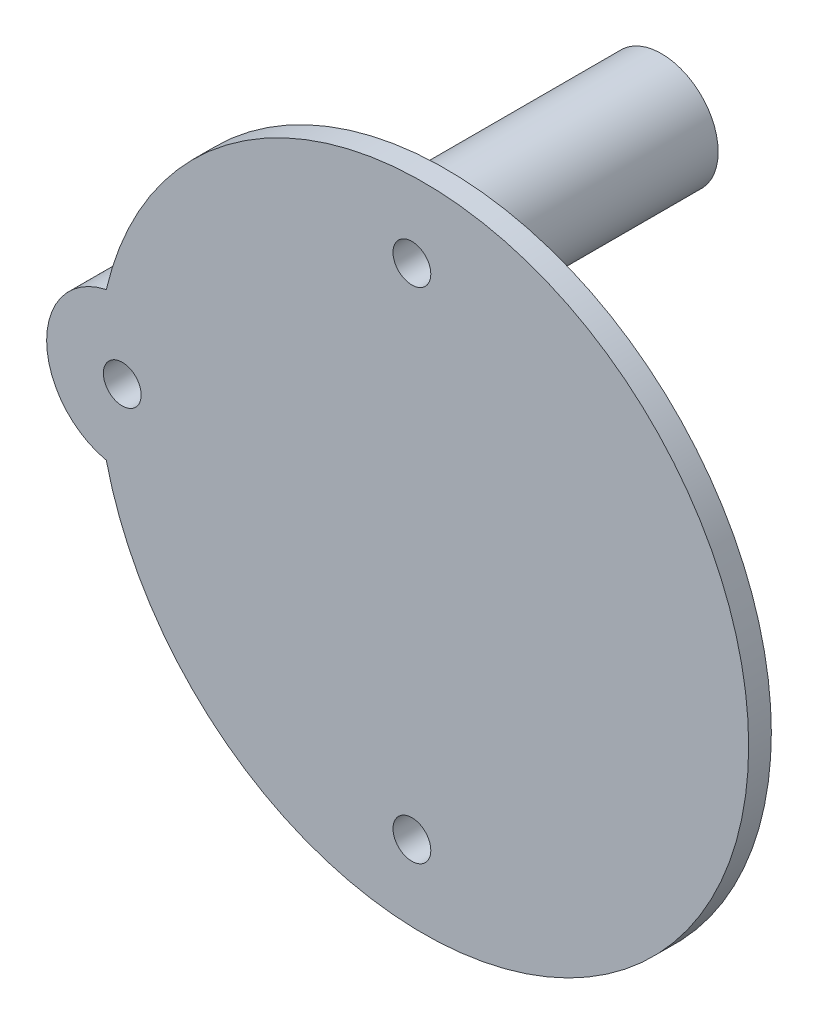
SolidWorks part; units mm, degrees
ref_plane "Front Plane" through (0, 0, 0) normal (0, 0, 1) x (1, 0, 0)
ref_plane "Top Plane" through (0, 0, 0) normal (0, 1, 0) x (1, 0, 0)
ref_plane "Right Plane" through (0, 0, 0) normal (1, 0, 0) x (0, 0, -1)
sketch "Sketch1" plane through (0, 0, 0) normal (0, 0, 1) x (1, 0, 0)
  circle A23 centre (29, 12) radius 5
  circle A24 centre (29, 12) radius 5
  circle A26 centre (-9.3, 45) radius 5
  circle A27 centre (-9.3, 45) radius 5
  circle A28 centre (29, 78) radius 7.5
  circle A29 centre (29, 78) radius 5
  circle A30 centre (29, 78) radius 5
  circle A31 centre (-9.3, 45) radius 10
  circle A34 centre (29, 12) radius 7
  dimension "D6" = 14
  dimension "D1" = 0.5
  dimension "D2" = 0.5
  dimension "D3" = 0.5
  dimension "D4" = 2.5
  dimension "D5" = 5
extrude "Boss-Extrude1" add sketch "Sketch1" along normal blind 3
sketch "Sketch3" plane through (0, 0, 3) normal (0, 0, 1) x (1, 0, 0)
  circle A0 centre (29, 12) radius 7 construction
  circle A1 centre (29, 78) radius 7.5 construction
  circle A2 centre (-9.3, 45) radius 10 construction
  circle A3 centre (29, 12) radius 7
  circle A4 centre (29, 78) radius 7.5
  circle A5 centre (-9.3, 45) radius 10
extrude "Boss-Extrude2" add sketch "Sketch3" along normal blind 27
sketch "Sketch4" plane through (0, 0, 30) normal (0, 0, 1) x (1, 0, 0)
  arc A0 (-11.4092, 35.225) -> (-11.4092, 54.775) centre (30.5, 45) ccw
  circle A3 centre (-9.3, 45) radius 10
  arc A4 (-11.4092, 54.775) -> (-11.4092, 35.225) centre (-9.3, 45) ccw
  dimension "D1" = 0
extrude "Boss-Extrude3" add sketch "Sketch4" along normal blind 3
sketch "Sketch5" plane through (0, 0, 33) normal (0, 0, 1) x (1, 0, 0)
  circle A0 centre (-9.3, 45) radius 2.5
  circle A1 centre (29, 12) radius 2.5
  circle A2 centre (29, 78) radius 2.5
  dimension "D1" = 5
  dimension "D2" = 5
  dimension "D3" = 5
extrude "Cut-Extrude1" cut sketch "Sketch5" against normal through all
